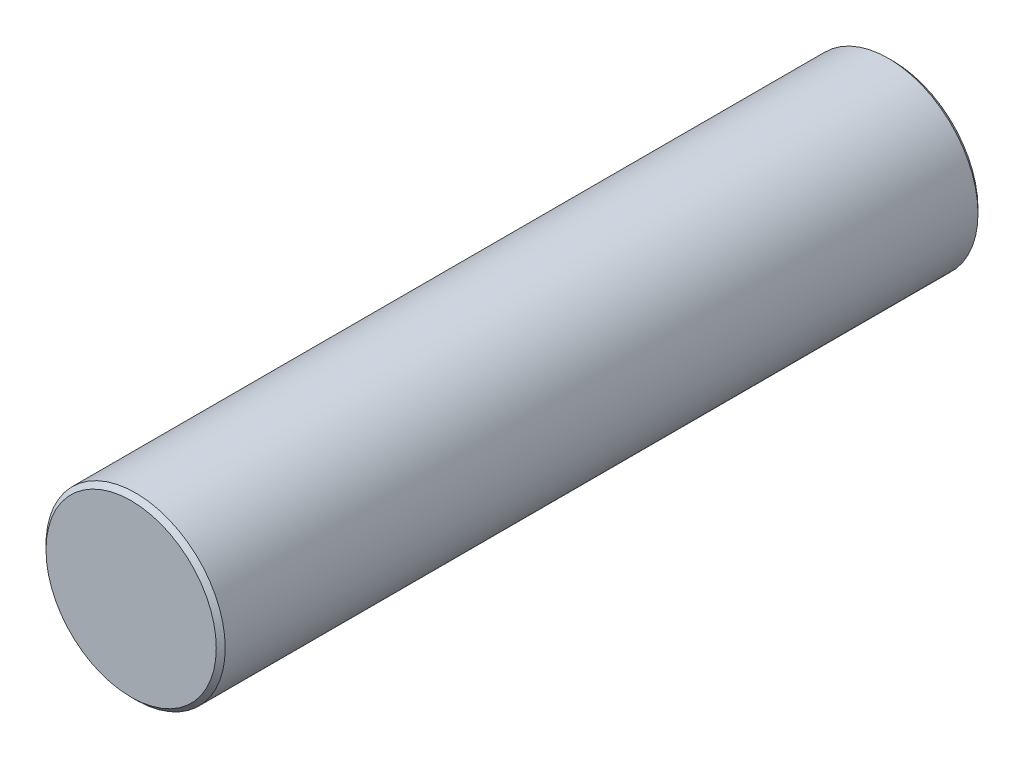
SolidWorks part; units mm, degrees
ref_plane "Front Plane" through (0, 0, 0) normal (0, 0, 1) x (1, 0, 0)
ref_plane "Top Plane" through (0, 0, 0) normal (0, 1, 0) x (1, 0, 0)
ref_plane "Right Plane" through (0, 0, 0) normal (1, 0, 0) x (0, 0, -1)
sketch "Sketch1" plane through (0, 0, 0) normal (0, 0, 1) x (1, 0, 0)
  circle A0 centre (0, 0) radius 20
  dimension "D1" = 40
extrude "Boss-Extrude1" add sketch "Sketch1" along normal blind 170
chamfer "Chamfer1" distance 1 angle 45 2 edges at (20, 0, 0) (20, 0, 170)
